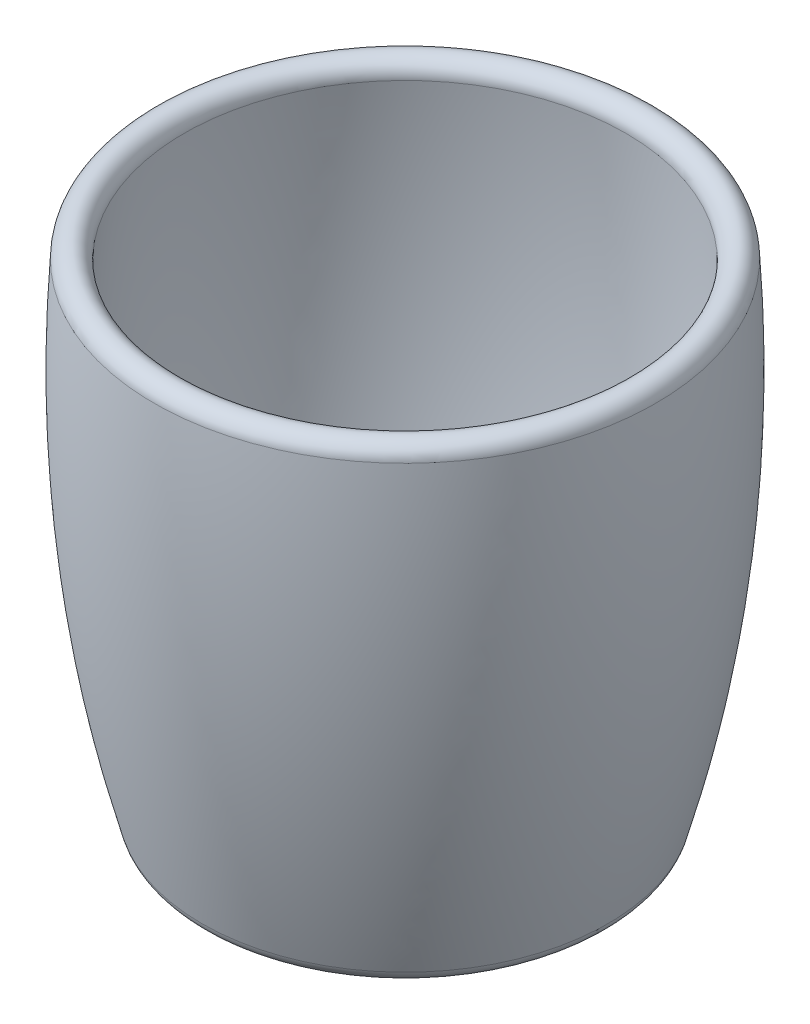
SolidWorks part; units mm, degrees
material "Plain Carbon Steel"
ref_plane "Front Plane" through (0, 0, 0) normal (0, 0, 1) x (1, 0, 0)
ref_plane "Top Plane" through (0, 0, 0) normal (0, 1, 0) x (1, 0, 0)
ref_plane "Right Plane" through (0, 0, 0) normal (1, 0, 0) x (0, 0, -1)
sketch "Sketch1" plane through (0, 0, 0) normal (0, 0, 1) x (1, 0, 0)
  line L0 (0, 0) -> (33.25, 0)
  line L5 (0, 0) -> (0, 83.0913) construction
  line L6 (40, 0) -> (40, 89.8747) construction
  line L7 (55.8118, 78.6822) -> (10.6882, -78.6822) construction
  line L8 (0, 5) -> (29.4504, 5)
  line L9 (0, 0) -> (0, 5)
  arc A0 (41.85, 81.4) -> (36.8601, 81.0819) centre (39.3551, 81.241) ccw
  spline S0 degree 3 poles (33.25, 0) (40.7706, 26.2274) (43.6373, 53.3607) (41.85, 81.4) knots 0 0 0 0 1 1 1 1
  spline S1 degree 1 poles (29.4504, 5) (36.8601, 81.0819) knots 0 0 1 1 construction
  spline S2 degree 3 poles (29.4504, 5) (31.0987, 11.1227) (33.8901, 23.5135) (36.5163, 42.3627) (37.4144, 58.3464) (37.3573, 71.2745) (37.0678, 77.8233) (36.8601, 81.0819) knots 0.046951 0.046951 0.046951 0.046951 0.285214 0.523476 0.761738 0.880869 1 1 1 1
  point P4 (40.0818, 32.2)
  dimension "D3" = 66.5
  dimension "D1" = 81.4
  dimension "D2" = 83.7
  dimension "D4" = 32.2
  dimension "D5" = 40
  dimension "D6" = 74
  dimension "D8" = 81.241
  dimension "D7" = 5
revolve "Revolve1" add sketch "Sketch1" angle 360 about L5
fillet "Fillet1" radius 3 2 edges at (0, 5, -29.4504) (0, 0, -33.25)
